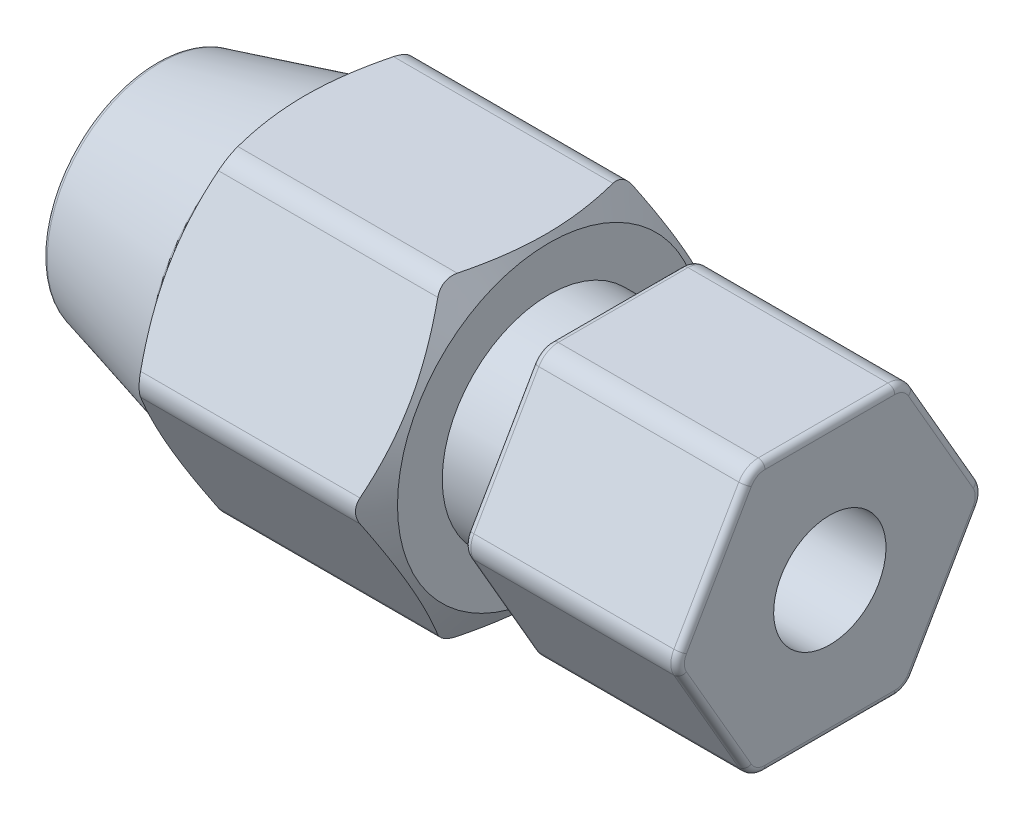
SolidWorks part; units mm, degrees
material "Никель"
ref_plane "Спереди" through (0, 0, 0) normal (0, 0, 1) x (1, 0, 0)
ref_plane "Сверху" through (0, 0, 0) normal (0, 1, 0) x (1, 0, 0)
ref_plane "Справа" through (0, 0, 0) normal (1, 0, 0) x (0, 0, -1)
sketch "Эскиз1" plane through (0, 0, 0) normal (0, 0, 1) x (1, 0, 0)
  line L0 (0, 0) -> (0, 40) construction
  line L1 (0, 0) -> (0, -40) construction
  line L2 (468.7338, 1006.8448) -> (2582.7338, 1006.8448) construction
  line L3 (0, 34.2239) -> (-29.6999, 34.2239) construction
  line L4 (0, 34.2239) -> (0, 40)
  line L5 (-9.5, 38.9739) -> (-9.5, 46.7239)
  line L6 (-9.5, 46.7239) -> (0, 46.7239)
  line L7 (-9.5, 38.9739) -> (-12.5, 38.9739)
  line L8 (-12.5, 38.9739) -> (-12.5, 40.9656)
  line L9 (-12.5, 40.9656) -> (-15.8246, 46.7239)
  line L10 (-15.8246, 46.7239) -> (-20.1754, 46.7239)
  line L11 (-20.1754, 46.7239) -> (-23.5, 40.9656)
  line L12 (-23.5, 40.9656) -> (-30, 39.2239)
  line L13 (-30, 39.2239) -> (-30, 38.4739)
  line L14 (-30, 38.4739) -> (-27.5, 38.4739)
  line L15 (-27.5, 38.4739) -> (-27.5, 37.6926)
  line L16 (-27.5, 37.6926) -> (-30, 37.4739)
  line L17 (-30, 37.4739) -> (-30, 36.7239)
  line L18 (-30, 36.7239) -> (0, 36.7239)
  line L19 (-12.5, 40.9656) -> (-23.5, 40.9656) construction
  line L20 (-9.5, 38.9739) -> (0, 38.9739) construction
  line L21 (0, 46.7239) -> (0, 38.9739)
  point P26 (-4.8671, 40.2958)
  dimension "D1" = 80
  dimension "D2" = 30
  dimension "D4" = 60
  dimension "D5" = 9.5
  dimension "D6" = 9.5
  dimension "D7" = 3
  dimension "D8" = 15
  dimension "D9" = 0.75
  dimension "D10" = 0.75
  dimension "D11" = 5
  dimension "D12" = 2.5
  dimension "D13" = 1
  dimension "D14" = 5
  dimension "D15" = 11
  dimension "D16" = 25
revolve "Повернуть1" add sketch "Эскиз1" angle 360 about L3
sketch "Эскиз2" plane through (-12.5, 0, 0) normal (1, 0, 0) x (0, 0, -1)
  line L1 (3.4641, 28.2239) -> (6.9282, 34.2239)
  line L2 (6.9282, 34.2239) -> (3.4641, 40.2239)
  line L3 (3.4641, 40.2239) -> (-3.4641, 40.2239)
  line L4 (-3.4641, 40.2239) -> (-6.9282, 34.2239)
  line L5 (-6.9282, 34.2239) -> (-3.4641, 28.2239)
  line L6 (-3.4641, 28.2239) -> (3.4641, 28.2239)
  circle A0 centre (0, 34.2239) radius 6 construction
  circle A1 centre (0, 34.2239) radius 12.5
  dimension "D2" = 25
  dimension "D1" = 12
extrude "Вырез-Вытянуть1" cut sketch "Эскиз2" along normal through all
fillet "Скругление1" radius 1 6 edges at (-4.75, 34.2239, -6.9282) (-4.75, 28.2239, -3.4641) (-4.75, 28.2239, 3.4641) (-4.75, 34.2239, 6.9282) (-4.75, 40.2239, -3.4641) (-4.75, 40.2239, 3.4641)
sketch "Эскиз3" plane through (-12.5, 0, 0) normal (1, 0, 0) x (0, 0, -1)
  line L1 (-4.0415, 27.2239) -> (4.0415, 27.2239)
  line L2 (4.0415, 27.2239) -> (8.0829, 34.2239)
  line L3 (8.0829, 34.2239) -> (4.0415, 41.2239)
  line L4 (4.0415, 41.2239) -> (-4.0415, 41.2239)
  line L5 (-4.0415, 41.2239) -> (-8.0829, 34.2239)
  line L6 (-8.0829, 34.2239) -> (-4.0415, 27.2239)
  circle A0 centre (0, 34.2239) radius 7 construction
  circle A1 centre (0, 34.2239) radius 12.5
  dimension "D2" = 25
  dimension "D1" = 14
extrude "Вырез-Вытянуть2" cut sketch "Эскиз3" against normal through all
fillet "Скругление2" radius 0.3 29 edges at (0, 34.2239, 6.7735) (0, 37.2239, 5.1962) (0, 40.0899, 3.3868) (0, 40.2239, 0) (0, 40.0899, -3.3868) (0, 37.2239, -5.1962) (0, 34.2239, -6.7735) (0, 31.2239, -5.1962) (0, 28.3579, -3.3868) (0, 28.2239, 0) (0, 28.3579, 3.3868) (-9.5, 28.3579, 3.3868) (-9.5, 28.2239, 0) (-9.5, 28.3579, -3.3868) (-9.5, 31.2239, -5.1962) (-9.5, 34.2239, -6.7735) (-9.5, 37.2239, -5.1962) (-9.5, 40.0899, -3.3868) (-9.5, 40.2239, 0) (-9.5, 40.0899, 3.3868) (-9.5, 37.2239, 5.1962) (-9.5, 34.2239, 6.7735) (0, 31.2239, 5.1962) (-9.5, 31.2239, 5.1962) (-9.5, 38.9739, 0) (-23.5, 40.9656, 0) (-30, 36.7239, 0) (-30, 37.4739, 0) (-30, 39.2239, 0)
fillet "Скругление3" radius 1 6 edges at (-18, 27.2239, 4.0415) (-18, 27.2239, -4.0415) (-18, 34.2239, -8.0829) (-18, 41.2239, -4.0415) (-18, 41.2239, 4.0415) (-18, 34.2239, 8.0829)
fillet "Скругление4" radius 0.15 1 edges at (-30, 38.4739, 0)
sketch "Эскиз4" plane through (0, 0, 0) normal (1, 0, 0) x (0, 0, -1)
  point P0 (0, 34.2239)
